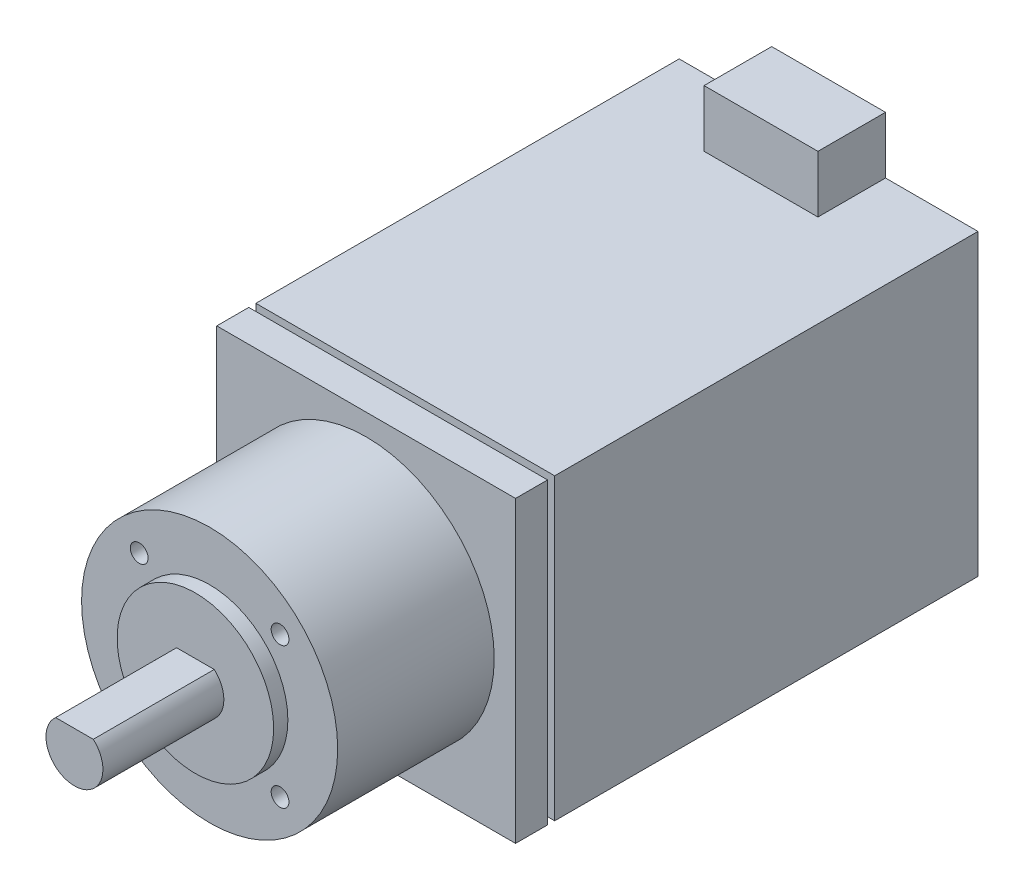
SolidWorks part; units mm, degrees
ref_plane "前视基准面" through (0, 0, 0) normal (0, 0, 1) x (1, 0, 0)
ref_plane "上视基准面" through (0, 0, 0) normal (0, 1, 0) x (1, 0, 0)
ref_plane "右视基准面" through (0, 0, 0) normal (1, 0, 0) x (0, 0, -1)
sketch "草图1" plane through (0, 0, 0) normal (0, 0, 1) x (1, 0, 0)
  line L1 (-21, 21) -> (21, 21)
  line L2 (-21, 21) -> (-21, -21)
  line L3 (-21, -21) -> (21, -21)
  line L4 (21, 21) -> (21, -21)
  line L5 (-21, 21) -> (21, -21) construction
  line L6 (-21, -21) -> (21, 21) construction
  point P0 (0, 0)
  dimension "D1" = 42
  dimension "D2" = 42
extrude "凸台-拉伸1" add sketch "草图1" along normal blind 65
sketch "草图2" plane through (0, 0, 65) normal (0, 0, 1) x (1, 0, 0)
  circle A0 centre (0, 0) radius 18
  dimension "D1" = 36
extrude "凸台-拉伸2" add sketch "草图2" along normal blind 22
sketch "草图3" plane through (0, 0, 87) normal (0, 0, 1) x (1, 0, 0)
  line L0 (-2.6458, 3) -> (2.6458, 3)
  arc A0 (-2.6458, 3) -> (2.6458, 3) centre (0, 0) ccw
  dimension "D1" = 8
  dimension "D2" = 1
extrude "凸台-拉伸3" add sketch "草图3" along normal blind 19
sketch "草图4" plane through (0, 0, 87) normal (0, 0, 1) x (1, 0, 0)
  circle A0 centre (0, 0) radius 11
  dimension "D1" = 22
extrude "凸台-拉伸4" add sketch "草图4" along normal blind 2
sketch "草图6" plane through (0, 21, 0) normal (0, 1, 0) x (1, 0, 0)
  line L0 (-21, -60) -> (21, -60) construction
  line L1 (-21, -65) -> (-21, 0) construction
  line L2 (21, -65) -> (21, 0) construction
  line L3 (21, -65) -> (-21, -65) construction
  line L5 (-21.5, -59.5) -> (21.5, -59.5)
  line L6 (-21.5, -59.5) -> (-21.5, -60.5)
  line L7 (-21.5, -60.5) -> (21.5, -60.5)
  line L8 (21.5, -59.5) -> (21.5, -60.5)
  line L9 (-21.5, -59.5) -> (21.5, -60.5) construction
  line L10 (-21.5, -60.5) -> (21.5, -59.5) construction
  point P8 (0, -60)
  dimension "D1" = 5
  dimension "D2" = 1
  dimension "D3" = 43
extrude "切除-拉伸1" cut sketch "草图6" against normal blind 2
pattern_circular "阵列(圆周)1" count 4 every 90 about axis through (0, 0, 0) along (0, 0, 1) of "切除-拉伸1"
sketch "草图7" plane through (0, 0, 87) normal (0, 0, 1) x (1, 0, 0)
  line L0 (-14, 0) -> (0, 0) construction
  line L1 (0, 0) -> (0, 14) construction
  line L2 (-9.8995, 9.8995) -> (0, 0) construction
  line L3 (9.8995, 9.8995) -> (0, 0) construction
  line L4 (9.8995, -9.8995) -> (0, 0) construction
  line L5 (-9.8995, -9.8995) -> (0, 0) construction
  circle A0 centre (0, 0) radius 14 construction
  point P4 (-9.8995, 9.8995)
  point P13 (0, 0)
  dimension "D1" = 28
  dimension "D2" = 45
  dimension "D3" = 4
hole_wizard "M3 螺纹孔1" positions "3D草图1" profile "草图8" tap size "M3" standard "GB"
sketch3d "3D草图1"
  point P0 (-9.8995, 9.8995, 87)
  point P3 (-9.8995, -9.8995, 87)
  point P6 (9.8995, 9.8995, 87)
  point P9 (9.8995, -9.8995, 87)
sketch "草图8" plane through (-9.8995, 9.8995, 87) normal (1, 0, 0) x (0, -1, 0)
  line L0 (0, 0) -> (0, 8.2511)
  line L1 (0, 8.2511) -> (1.25, 7.5)
  line L2 (1.25, 7.5) -> (1.25, 0)
  line L5 (1.25, 0) -> (0, 0)
  line L10 (0, 8.2511) -> (-1.25, 7.5) construction
  line L11 (0, -6.35) -> (0, 107.95) construction
  dimension "螺纹孔钻头直径" = 2.5
  dimension "螺纹孔钻头深度" = 7.5
  dimension "导头角度" = 118
cosmetic thread "孔螺蚊线1" parameters "D1"=6, "D2"=3
cosmetic thread "孔螺蚊线2" parameters "D1"=6, "D2"=3
cosmetic thread "孔螺蚊线3" parameters "D1"=6, "D2"=3
cosmetic thread "孔螺蚊线4" parameters "D1"=6, "D2"=3
sketch "草图9" plane through (0, 21, 0) normal (0, 1, 0) x (1, 0, 0)
  line L0 (0, 0) -> (0, -59.5) construction
  line L1 (21, -59.5) -> (-21, -59.5) construction
  line L2 (21, 0) -> (-21, 0) construction
  line L3 (-8, -9.5) -> (8, -9.5)
  line L4 (-8, -9.5) -> (-8, 0)
  line L5 (-8, 0) -> (8, 0)
  line L6 (8, -9.5) -> (8, 0)
  line L7 (-8, -9.5) -> (8, 0) construction
  line L8 (-8, 0) -> (8, -9.5) construction
  point P5 (0, -4.75)
  dimension "D1" = 16
  dimension "D2" = 9.5
extrude "凸台-拉伸5" add sketch "草图9" along normal blind 8
